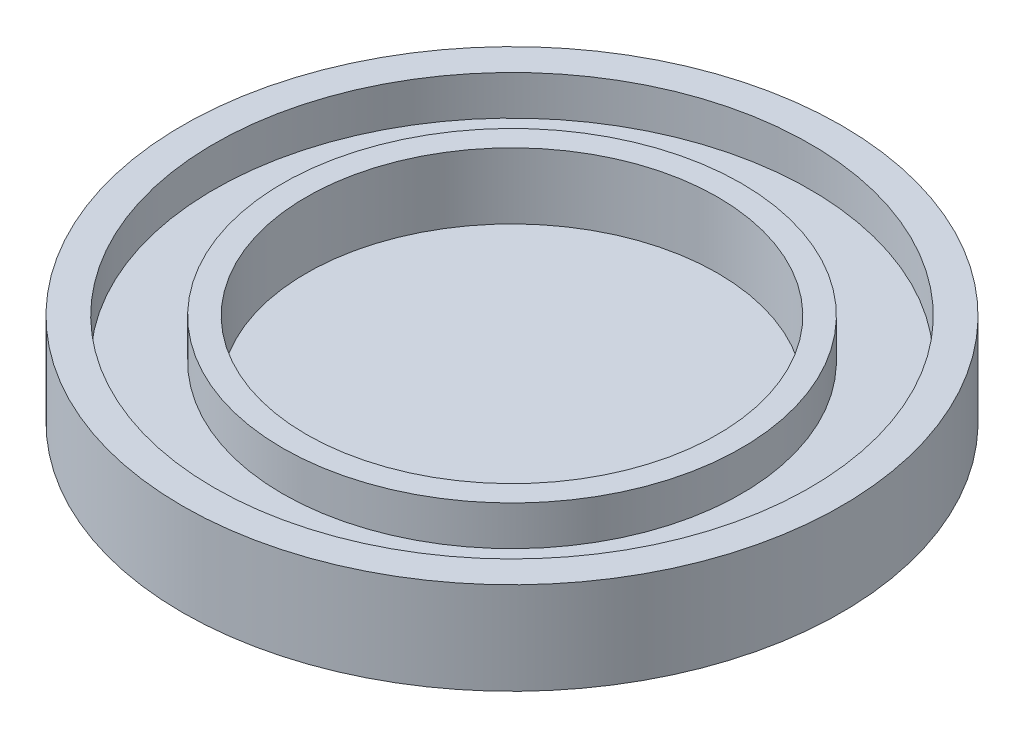
SolidWorks part; units mm, degrees
ref_plane "Plan de face" through (0, 0, 0) normal (0, 0, 1) x (1, 0, 0)
ref_plane "Plan de dessus" through (0, 0, 0) normal (0, 1, 0) x (1, 0, 0)
ref_plane "Plan de droite" through (0, 0, 0) normal (1, 0, 0) x (0, 0, -1)
sketch "Esquisse2" plane through (0, 0, 0) normal (0, 1, 0) x (1, 0, 0)
  circle A0 centre (0, 0) radius 25
  dimension "D1" = 50
extrude "Boss.-Extru.1" add sketch "Esquisse2" along normal blind 7
sketch "Esquisse3" plane through (0, 7, 0) normal (0, 1, 0) x (1, 0, 0)
  circle A0 centre (0, 0) radius 15.6
  dimension "D1" = 31.2
extrude "Enlèv. mat.-Extru.1" cut sketch "Esquisse3" against normal blind 5
sketch "Esquisse5" plane through (0, 7, 0) normal (0, 1, 0) x (1, 0, 0)
  circle A0 centre (0, 0) radius 17.4
  circle A1 centre (0, 0) radius 22.6
  dimension "D1" = 34.8
  dimension "D2" = 45.2
extrude "Enlèv. mat.-Extru.2" cut sketch "Esquisse5" against normal blind 3
